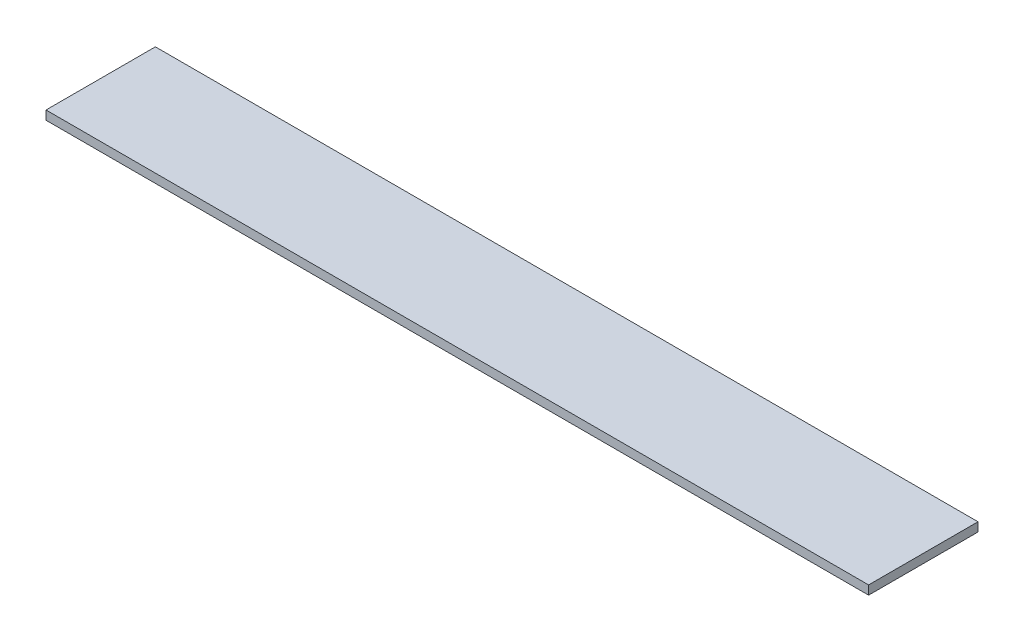
SolidWorks part; units mm, degrees
ref_plane "Front Plane" through (0, 0, 0) normal (0, 0, 1) x (1, 0, 0)
ref_plane "Top Plane" through (0, 0, 0) normal (0, 1, 0) x (1, 0, 0)
ref_plane "Right Plane" through (0, 0, 0) normal (1, 0, 0) x (0, 0, -1)
sketch "Sketch1" plane through (0, 0, 0) normal (0, 1, 0) x (1, 0, 0)
  line L1 (0, 0) -> (92.5, 0)
  line L2 (0, 0) -> (0, 12.3)
  line L3 (0, 12.3) -> (92.5, 12.3)
  line L4 (92.5, 0) -> (92.5, 12.3)
  dimension "D1" = 12.3
  dimension "D2" = 92.5
extrude "Boss-Extrude1" add sketch "Sketch1" along normal blind 1
